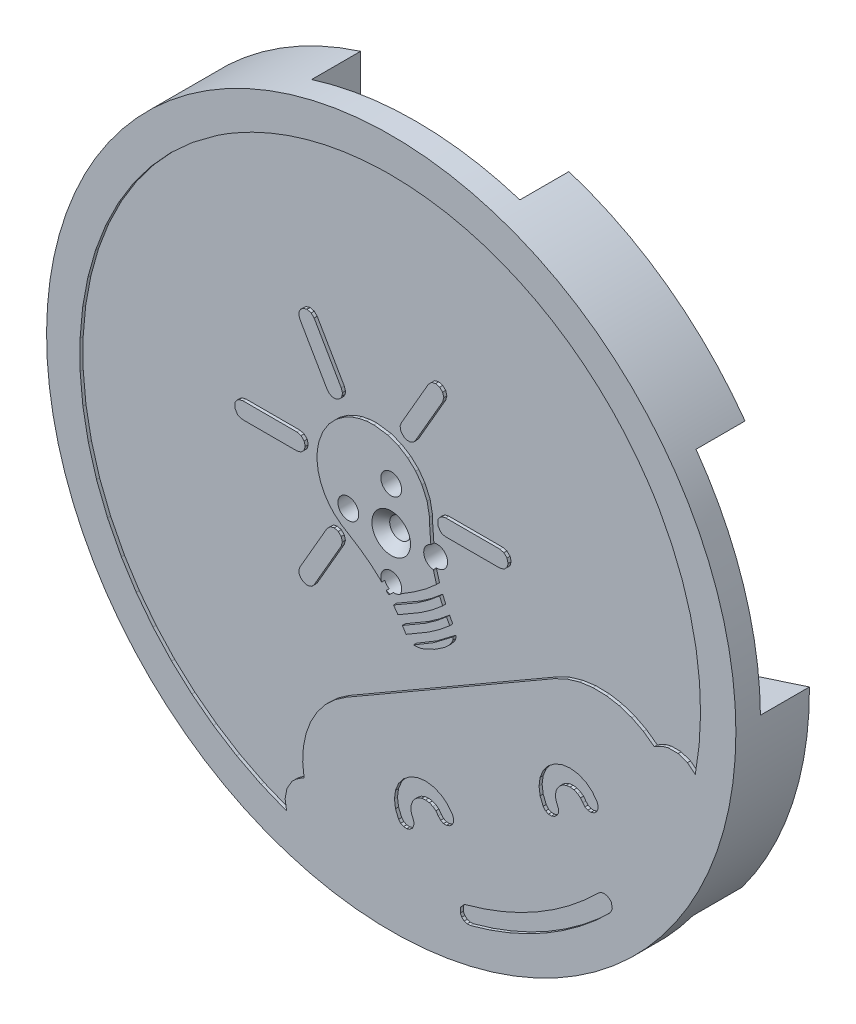
SolidWorks part; units mm, degrees
ref_plane "Front Plane" through (0, 0, 0) normal (0, 0, 1) x (1, 0, 0)
ref_plane "Top Plane" through (0, 0, 0) normal (0, 1, 0) x (1, 0, 0)
ref_plane "Right Plane" through (0, 0, 0) normal (1, 0, 0) x (0, 0, -1)
sketch "Sketch2" plane through (0, 0, 0) normal (0, 0, 1) x (1, 0, 0)
  line L0 (0, 10) -> (0, 0) construction
  line L1 (0, 0) -> (0, -10) construction
  line L3 (0, -10) -> (0, -56.25) construction
  line L4 (-56.25, 0) -> (-10, 0) construction
  line L5 (-10, 0) -> (0, 0) construction
  line L6 (0, 0) -> (10, 0) construction
  line L7 (10, 0) -> (56.25, 0) construction
  line L8 (0, 56.25) -> (0, 34.65) construction
  line L9 (0, 34.65) -> (0, 10) construction
  circle A0 centre (0, 0) radius 56.25
  point P6 (0, -33.125)
  point P8 (0, 34.65)
  point P13 (-33.125, 0)
  point P14 (33.125, 0)
  dimension "D1" = 112.5
  dimension "D2" = 20
  dimension "D3" = 21.6
extrude "Boss-Extrude1" add sketch "Sketch2" along normal blind 12
sketch "Sketch3" plane through (0, 0, 0) normal (0, 0, -1) x (-1, 0, 0)
  line L1 (-17, 34.65) -> (-17, 53.6196)
  line L2 (17, 34.65) -> (17, 53.6196)
  arc A0 (-17, 34.65) -> (17, 34.65) centre (0, 34.65) ccw
  circle A2 centre (0, 0) radius 56.25 construction
  arc A10 (17, 53.6196) -> (-17, 53.6196) centre (0, 0) ccw
  dimension "D1" = 34
sketch "Sketch4" plane through (0, 0, 0) normal (0, 0, -1) x (-1, 0, 0)
  line L0 (-10, 0) -> (-7, 0) construction
  line L1 (-7, 0) -> (0, 0) construction
  line L2 (0, 0) -> (7, 0) construction
  line L3 (7, 0) -> (10, 0) construction
  line L4 (0, -10) -> (0, -7) construction
  line L5 (0, -7) -> (0, 0) construction
  line L6 (0, 0) -> (0, 7) construction
  line L7 (0, 7) -> (0, 10) construction
  circle A0 centre (0, 0) radius 10
  dimension "D1" = 20
  dimension "D2" = 14
extrude "Cut-Extrude2" cut sketch "Sketch4" against normal blind 2
hole_wizard "M3 Clearance Hole1" positions "Sketch5" profile "Sketch6" hole size "M3" standard "ANSI Metric"
sketch "Sketch5" plane through (0, 0, 2) normal (0, 0, -1) x (-1, 0, 0)
  point P0 (7, 0)
  point P3 (0, 7)
  point P6 (-7, 0)
  point P9 (0, -7)
sketch "Sketch6" plane through (-7, 0, 2) normal (1, 0, 0) x (0, 1, 0)
  line L0 (0, 0) -> (0, 11.0215)
  line L1 (0, 11.0215) -> (1.7, 10)
  line L2 (1.7, 10) -> (1.7, 0)
  line L5 (1.7, 0) -> (0, 0)
  line L10 (0, 11.0215) -> (-1.7, 10) construction
  line L11 (0, -6.35) -> (0, 107.95) construction
  dimension "Hole Dia." = 3.4
  dimension "Hole Depth" = 10
  dimension "Drill Angle" = 118
hole_wizard "CSK for M3 Flat Head Machine Screw2" positions "Sketch9" profile "Sketch10" countersink size "M3" standard "ANSI Metric"
sketch "Sketch9" plane through (0, 0, 12) normal (0, 0, 1) x (1, 0, 0)
  point P0 (0, 0)
sketch "Sketch10" plane through (0, 0, 12) normal (1, 0, 0) x (0, -1, 0)
  line L0 (0, 0) -> (0, 11.0215)
  line L1 (0, 11.0215) -> (1.7, 10)
  line L2 (1.7, 10) -> (1.7, 1.45)
  line L3 (1.7, 1.45) -> (3.15, 0)
  line L5 (3.15, 0) -> (0, 0)
  line L6 (-1.7, 1.45) -> (-3.15, 0) construction
  line L10 (0, 11.0215) -> (-1.7, 10) construction
  line L11 (0, -6.35) -> (0, 107.95) construction
  dimension "Hole Dia." = 3.4
  dimension "Hole Depth" = 10
  dimension "Near C'Sink Dia." = 6.3
  dimension "Near C'Sink Angle" = 90
  dimension "Drill Angle" = 118
extrude "Cut-Extrude3" cut sketch "Sketch3" against normal blind 8
pattern_circular "CirPattern1" count 5 over 360 about axis through (0, 0, 0) along (0, 0, 1) of "Cut-Extrude3"
sketch "Sketch11" plane through (0, 0, 8) normal (0, 0, -1) x (-1, 0, 0)
  circle A0 centre (0, 34.65) radius 5.25
  dimension "D1" = 10.5
extrude "Cut-Extrude4" cut sketch "Sketch11" against normal blind 2.5
sketch "Sketch12" plane through (0, 0, 12) normal (0, 0, 1) x (1, 0, 0)
  line L0 (43.7235, 25.2994) -> (42.8623, 26.7358)
  line L1 (42.8623, 26.7358) -> (41.9454, 28.1541)
  line L2 (41.9454, 28.1541) -> (40.1116, 30.7156)
  line L3 (40.1116, 30.7156) -> (38.1348, 33.1435)
  line L4 (38.1348, 33.1435) -> (36.0227, 35.4332)
  line L5 (36.0227, 35.4332) -> (33.7829, 37.5804)
  line L6 (33.7829, 37.5804) -> (31.4231, 39.5807)
  line L7 (31.4231, 39.5807) -> (28.9511, 41.4296)
  line L8 (28.9511, 41.4296) -> (26.3743, 43.1228)
  line L9 (26.3743, 43.1228) -> (23.7005, 44.6558)
  line L10 (23.7005, 44.6558) -> (20.9373, 46.0242)
  line L11 (20.9373, 46.0242) -> (18.0925, 47.2236)
  line L12 (18.0925, 47.2236) -> (15.1736, 48.2497)
  line L13 (15.1736, 48.2497) -> (12.1883, 49.0979)
  line L14 (12.1883, 49.0979) -> (9.1442, 49.7639)
  line L15 (9.1442, 49.7639) -> (6.0491, 50.2433)
  line L16 (6.0491, 50.2433) -> (2.9106, 50.5316)
  line L17 (2.9106, 50.5316) -> (-0.2637, 50.6245)
  line L18 (-0.2637, 50.6245) -> (-1.3593, 50.6106)
  line L19 (-1.3593, 50.6106) -> (-4.53, 50.4362)
  line L20 (-4.53, 50.4362) -> (-7.6743, 50.0649)
  line L21 (-7.6743, 50.0649) -> (-10.7834, 49.4994)
  line L22 (-10.7834, 49.4994) -> (-13.8483, 48.742)
  line L23 (-13.8483, 48.742) -> (-16.86, 47.7953)
  line L24 (-16.86, 47.7953) -> (-19.8098, 46.6618)
  line L25 (-19.8098, 46.6618) -> (-22.6886, 45.344)
  line L26 (-22.6886, 45.344) -> (-25.4876, 43.8444)
  line L27 (-25.4876, 43.8444) -> (-25.5072, 43.8331)
  line L28 (-25.5072, 43.8331) -> (-25.5139, 43.8293)
  line L29 (-25.5139, 43.8293) -> (-26.569, 43.2016)
  line L30 (-26.569, 43.2016) -> (-26.7302, 43.1028)
  line L31 (-26.7302, 43.1028) -> (-27.5612, 42.5798)
  line L32 (-27.5612, 42.5798) -> (-27.5669, 42.5765)
  line L33 (-27.5669, 42.5765) -> (-28.0151, 42.2833)
  line L34 (-28.0151, 42.2833) -> (-28.4549, 41.9912)
  line L35 (-28.4549, 41.9912) -> (-32.4156, 39.0373)
  line L36 (-32.4156, 39.0373) -> (-36.011, 35.7728)
  line L37 (-36.011, 35.7728) -> (-39.2342, 32.2285)
  line L38 (-39.2342, 32.2285) -> (-42.0781, 28.435)
  line L39 (-42.0781, 28.435) -> (-44.5355, 24.4229)
  line L40 (-44.5355, 24.4229) -> (-46.5993, 20.2229)
  line L41 (-46.5993, 20.2229) -> (-48.2626, 15.8657)
  line L42 (-48.2626, 15.8657) -> (-49.5181, 11.3819)
  line L43 (-49.5181, 11.3819) -> (-50.3588, 6.8022)
  line L44 (-50.3588, 6.8022) -> (-50.7776, 2.1572)
  line L45 (-50.7776, 2.1572) -> (-50.7675, -2.5225)
  line L46 (-50.7675, -2.5225) -> (-50.3212, -7.2061)
  line L47 (-50.3212, -7.2061) -> (-49.4318, -11.863)
  line L48 (-49.4318, -11.863) -> (-48.0921, -16.4626)
  line L49 (-48.0921, -16.4626) -> (-46.2951, -20.9742)
  line L50 (-46.2951, -20.9742) -> (-44.0336, -25.3672)
  line L51 (-44.0336, -25.3672) -> (-41.6099, -29.1646)
  line L52 (-41.6099, -29.1646) -> (-38.8754, -32.7114)
  line L53 (-38.8754, -32.7114) -> (-35.8505, -35.9908)
  line L54 (-35.8505, -35.9908) -> (-32.5551, -38.9862)
  line L55 (-32.5551, -38.9862) -> (-29.0095, -41.6806)
  line L56 (-29.0095, -41.6806) -> (-25.2338, -44.0575)
  line L57 (-25.2338, -44.0575) -> (-21.2482, -46.1)
  line L58 (-21.2482, -46.1) -> (-17.0728, -47.7914)
  line L59 (-17.0728, -47.7914) -> (-17.32, -46.1638)
  line L60 (-17.32, -46.1638) -> (-17.0163, -44.577)
  line L61 (-17.0163, -44.577) -> (-16.1985, -43.1708)
  line L62 (-16.1985, -43.1708) -> (-15.6084, -42.5793)
  line L63 (-15.6084, -42.5793) -> (-14.9035, -42.0854)
  line L64 (-14.9035, -42.0854) -> (-14.2254, -41.6946)
  line L65 (-14.2254, -41.6946) -> (-14.4481, -39.532)
  line L66 (-14.4481, -39.532) -> (-14.3405, -37.3819)
  line L67 (-14.3405, -37.3819) -> (-13.9125, -35.2814)
  line L68 (-13.9125, -35.2814) -> (-13.1741, -33.2679)
  line L69 (-13.1741, -33.2679) -> (-12.1352, -31.3787)
  line L70 (-12.1352, -31.3787) -> (-10.8059, -29.6512)
  line L71 (-10.8059, -29.6512) -> (-9.1961, -28.1226)
  line L72 (-9.1961, -28.1226) -> (-7.3158, -26.8303)
  line L73 (-7.3158, -26.8303) -> (26.5969, -7.2521)
  line L74 (26.5969, -7.2521) -> (28.6562, -6.2697)
  line L75 (28.6562, -6.2697) -> (30.7847, -5.6397)
  line L76 (30.7847, -5.6397) -> (32.9452, -5.352)
  line L77 (32.9452, -5.352) -> (35.1004, -5.3966)
  line L78 (35.1004, -5.3966) -> (37.2131, -5.7635)
  line L79 (37.2131, -5.7635) -> (39.2459, -6.4429)
  line L80 (39.2459, -6.4429) -> (41.1616, -7.4246)
  line L81 (41.1616, -7.4246) -> (42.923, -8.6987)
  line L82 (42.923, -8.6987) -> (43.6019, -8.308)
  line L83 (43.6019, -8.308) -> (44.3813, -7.9447)
  line L84 (44.3813, -7.9447) -> (45.1879, -7.7291)
  line L85 (45.1879, -7.7291) -> (46.813, -7.7223)
  line L86 (46.813, -7.7223) -> (48.338, -8.2503)
  line L87 (48.338, -8.2503) -> (49.6234, -9.2755)
  line L88 (49.6234, -9.2755) -> (50.251, -4.8179)
  line L89 (50.251, -4.8179) -> (50.4804, -0.3486)
  line L90 (50.4804, -0.3486) -> (50.316, 4.1065)
  line L91 (50.316, 4.1065) -> (49.7622, 8.5218)
  line L92 (49.7622, 8.5218) -> (48.8234, 12.8715)
  line L93 (48.8234, 12.8715) -> (47.5039, 17.1299)
  line L94 (47.5039, 17.1299) -> (45.8082, 21.2713)
  line L95 (45.8082, 21.2713) -> (43.7406, 25.2698)
  line L96 (43.7406, 25.2698) -> (43.7235, 25.2994)
  line L97 (18.8919, 5.9467) -> (19.0715, 5.2506)
  line L98 (19.0715, 5.2506) -> (18.8841, 4.5994)
  line L99 (18.8841, 4.5994) -> (18.4047, 4.1205)
  line L100 (18.4047, 4.1205) -> (17.7085, 3.9415)
  line L101 (17.7085, 3.9415) -> (8.9061, 3.9412)
  line L102 (8.9061, 3.9412) -> (8.4238, 4.017)
  line L103 (8.4238, 4.017) -> (8.0375, 4.2346)
  line L104 (8.0375, 4.2346) -> (7.5907, 4.9484)
  line L105 (7.5907, 4.9484) -> (7.6407, 5.789)
  line L106 (7.6407, 5.789) -> (7.8754, 6.1652)
  line L107 (7.8754, 6.1652) -> (8.2623, 6.463)
  line L108 (8.2623, 6.463) -> (8.8865, 6.6177)
  line L109 (8.8865, 6.6177) -> (8.9065, 6.6172)
  line L110 (8.9065, 6.6172) -> (17.7069, 6.6177)
  line L111 (17.7069, 6.6177) -> (18.3911, 6.4443)
  line L112 (18.3911, 6.4443) -> (18.8918, 5.9468)
  line L113 (18.8918, 5.9468) -> (18.8919, 5.9467)
  line L114 (8.3841, 24.1347) -> (8.5767, 23.4467)
  line L115 (8.5767, 23.4467) -> (8.3879, 22.7576)
  line L116 (8.3879, 22.7576) -> (3.9874, 15.1352)
  line L117 (3.9874, 15.1352) -> (3.5976, 14.6654)
  line L118 (3.5976, 14.6654) -> (3.1217, 14.4439)
  line L119 (3.1217, 14.4439) -> (2.617, 14.4375)
  line L120 (2.617, 14.4375) -> (2.141, 14.6132)
  line L121 (2.141, 14.6132) -> (1.7509, 14.9378)
  line L122 (1.7509, 14.9378) -> (1.5042, 15.3782)
  line L123 (1.5042, 15.3782) -> (1.4583, 15.9011)
  line L124 (1.4583, 15.9011) -> (1.6706, 16.4735)
  line L125 (1.6706, 16.4735) -> (6.0707, 24.0956)
  line L126 (6.0707, 24.0956) -> (6.6071, 24.6229)
  line L127 (6.6071, 24.6229) -> (7.2307, 24.7818)
  line L128 (7.2307, 24.7818) -> (7.249, 24.781)
  line L129 (7.249, 24.781) -> (7.9008, 24.6058)
  line L130 (7.9008, 24.6058) -> (8.3841, 24.1347)
  line L131 (33.5794, -21.1232) -> (32.7665, -20.0667)
  line L132 (32.7665, -20.0667) -> (31.7242, -19.2693)
  line L133 (31.7242, -19.2693) -> (30.5123, -18.7655)
  line L134 (30.5123, -18.7655) -> (29.1908, -18.5899)
  line L135 (29.1908, -18.5899) -> (27.8691, -18.7655)
  line L136 (27.8691, -18.7655) -> (26.6569, -19.2694)
  line L137 (26.6569, -19.2694) -> (25.6142, -20.067)
  line L138 (25.6142, -20.067) -> (24.8011, -21.1236)
  line L139 (24.8011, -21.1236) -> (24.2926, -22.356)
  line L140 (24.2926, -22.356) -> (24.1233, -23.6576)
  line L141 (24.1233, -23.6576) -> (24.293, -24.9592)
  line L142 (24.293, -24.9592) -> (24.8017, -26.1916)
  line L143 (24.8017, -26.1916) -> (25.1928, -26.6515)
  line L144 (25.1928, -26.6515) -> (25.6667, -26.8677)
  line L145 (25.6667, -26.8677) -> (26.1675, -26.8724)
  line L146 (26.1675, -26.8724) -> (26.6394, -26.6979)
  line L147 (26.6394, -26.6979) -> (27.0265, -26.3765)
  line L148 (27.0265, -26.3765) -> (27.2728, -25.9404)
  line L149 (27.2728, -25.9404) -> (27.3226, -25.4219)
  line L150 (27.3226, -25.4219) -> (27.1198, -24.8532)
  line L151 (27.1198, -24.8532) -> (26.8788, -24.271)
  line L152 (26.8788, -24.271) -> (26.7984, -23.6577)
  line L153 (26.7984, -23.6577) -> (26.8785, -23.0444)
  line L154 (26.8785, -23.0444) -> (27.1192, -22.4622)
  line L155 (27.1192, -22.4622) -> (27.5031, -21.9625)
  line L156 (27.5031, -21.9625) -> (27.9943, -21.5862)
  line L157 (27.9943, -21.5862) -> (28.5658, -21.3489)
  line L158 (28.5658, -21.3489) -> (29.1905, -21.2664)
  line L159 (29.1905, -21.2664) -> (29.8152, -21.3489)
  line L160 (29.8152, -21.3489) -> (30.3865, -21.5861)
  line L161 (30.3865, -21.5861) -> (30.8776, -21.9623)
  line L162 (30.8776, -21.9623) -> (31.2614, -22.4621)
  line L163 (31.2614, -22.4621) -> (31.6154, -22.872)
  line L164 (31.6154, -22.872) -> (32.084, -23.1026)
  line L165 (32.084, -23.1026) -> (32.6051, -23.137)
  line L166 (32.6051, -23.137) -> (33.1164, -22.9587)
  line L167 (33.1164, -22.9587) -> (33.5098, -22.6012)
  line L168 (33.5098, -22.6012) -> (33.728, -22.1368)
  line L169 (33.728, -22.1368) -> (33.7561, -21.6244)
  line L170 (33.7561, -21.6244) -> (33.5792, -21.1232)
  line L171 (33.5792, -21.1232) -> (33.5794, -21.1232)
  line L172 (35.9136, -34.2086) -> (35.7019, -33.9343)
  line L173 (35.7019, -33.9343) -> (35.2582, -33.6402)
  line L174 (35.2582, -33.6402) -> (34.7536, -33.5425)
  line L175 (34.7536, -33.5425) -> (34.2493, -33.6411)
  line L176 (34.2493, -33.6411) -> (33.8061, -33.936)
  line L177 (33.8061, -33.936) -> (31.499, -36.0991)
  line L178 (31.499, -36.0991) -> (29.0626, -38.0994)
  line L179 (29.0626, -38.0994) -> (26.5058, -39.9318)
  line L180 (26.5058, -39.9318) -> (23.8373, -41.5911)
  line L181 (23.8373, -41.5911) -> (21.066, -43.0723)
  line L182 (21.066, -43.0723) -> (18.2006, -44.3703)
  line L183 (18.2006, -44.3703) -> (15.2501, -45.48)
  line L184 (15.2501, -45.48) -> (12.2231, -46.3963)
  line L185 (12.2231, -46.3963) -> (11.8899, -46.5358)
  line L186 (11.8899, -46.5358) -> (11.3288, -47.1827)
  line L187 (11.3288, -47.1827) -> (11.2738, -48.0372)
  line L188 (11.2738, -48.0372) -> (11.5102, -48.5142)
  line L189 (11.5102, -48.5142) -> (11.8976, -48.8517)
  line L190 (11.8976, -48.8517) -> (12.3834, -49.0194)
  line L191 (12.3834, -49.0194) -> (12.9147, -48.9866)
  line L192 (12.9147, -48.9866) -> (16.1107, -48.0191)
  line L193 (16.1107, -48.0191) -> (19.226, -46.8474)
  line L194 (19.226, -46.8474) -> (22.2515, -45.4768)
  line L195 (22.2515, -45.4768) -> (25.1777, -43.9128)
  line L196 (25.1777, -43.9128) -> (27.9953, -42.1608)
  line L197 (27.9953, -42.1608) -> (30.6951, -40.2261)
  line L198 (30.6951, -40.2261) -> (33.2676, -38.114)
  line L199 (33.2676, -38.114) -> (35.7035, -35.8301)
  line L200 (35.7035, -35.8301) -> (36.0844, -35.0551)
  line L201 (36.0844, -35.0551) -> (35.9136, -34.2086)
  line L202 (5.0001, 9.3752) -> (5.8508, 7.4638)
  line L203 (5.8508, 7.4638) -> (6.2496, 5.3897)
  line L204 (6.2496, 5.3897) -> (6.2659, 4.2834)
  line L205 (6.2659, 4.2834) -> (6.5775, -0.0444)
  line L206 (6.5775, -0.0444) -> (6.9114, -1.8586)
  line L207 (6.9114, -1.8586) -> (7.3817, -3.5473)
  line L208 (7.3817, -3.5473) -> (5.6898, -5.0138)
  line L209 (5.6898, -5.0138) -> (3.6505, -6.4723)
  line L210 (3.6505, -6.4723) -> (1.5139, -7.7977)
  line L211 (1.5139, -7.7977) -> (-0.4701, -8.8653)
  line L212 (-0.4701, -8.8653) -> (-1.7709, -7.4519)
  line L213 (-1.7709, -7.4519) -> (-3.2631, -6.1237)
  line L214 (-3.2631, -6.1237) -> (-5.0314, -4.8121)
  line L215 (-5.0314, -4.8121) -> (-7.1608, -3.4481)
  line L216 (-7.1608, -3.4481) -> (-8.109, -2.8817)
  line L217 (-8.109, -2.8817) -> (-9.2084, -1.9979)
  line L218 (-9.2084, -1.9979) -> (-10.1514, -0.9657)
  line L219 (-10.1514, -0.9657) -> (-10.9252, 0.1926)
  line L220 (-10.9252, 0.1926) -> (-11.5166, 1.4545)
  line L221 (-11.5166, 1.4545) -> (-11.9128, 2.7976)
  line L222 (-11.9128, 2.7976) -> (-12.1007, 4.1994)
  line L223 (-12.1007, 4.1994) -> (-12.0674, 5.6375)
  line L224 (-12.0674, 5.6375) -> (-11.7999, 7.0895)
  line L225 (-11.7999, 7.0895) -> (-11.1395, 8.8296)
  line L226 (-11.1395, 8.8296) -> (-10.174, 10.358)
  line L227 (-10.174, 10.358) -> (-8.9501, 11.6473)
  line L228 (-8.9501, 11.6473) -> (-7.5146, 12.6703)
  line L229 (-7.5146, 12.6703) -> (-6.4277, 13.206)
  line L230 (-6.4277, 13.206) -> (-5.275, 13.596)
  line L231 (-5.275, 13.596) -> (-4.0716, 13.8317)
  line L232 (-4.0716, 13.8317) -> (-2.8328, 13.9043)
  line L233 (-2.8328, 13.9043) -> (-0.5397, 13.5906)
  line L234 (-0.5397, 13.5906) -> (1.182, 12.9399)
  line L235 (1.182, 12.9399) -> (2.6961, 11.9911)
  line L236 (2.6961, 11.9911) -> (3.9773, 10.7881)
  line L237 (3.9773, 10.7881) -> (5.0001, 9.3752)
  line L238 (7.8894, -4.9172) -> (8.395, -6.0631)
  line L239 (8.395, -6.0631) -> (6.7815, -7.4143)
  line L240 (6.7815, -7.4143) -> (4.8994, -8.7462)
  line L241 (4.8994, -8.7462) -> (1.0949, -10.9729)
  line L242 (1.0949, -10.9729) -> (0.3738, -9.9489)
  line L243 (0.3738, -9.9489) -> (4.2522, -7.7051)
  line L244 (4.2522, -7.7051) -> (6.1793, -6.3429)
  line L245 (6.1793, -6.3429) -> (7.8894, -4.9172)
  line L246 (9.0128, -7.3161) -> (9.5437, -8.2953)
  line L247 (9.5437, -8.2953) -> (7.9562, -9.6109)
  line L248 (7.9562, -9.6109) -> (6.1212, -10.9052)
  line L249 (6.1212, -10.9052) -> (2.4134, -13.0803)
  line L250 (2.4134, -13.0803) -> (1.8236, -12.116)
  line L251 (1.8236, -12.116) -> (5.5241, -9.9638)
  line L252 (5.5241, -9.9638) -> (7.3622, -8.6707)
  line L253 (7.3622, -8.6707) -> (9.0128, -7.3161)
  line L254 (10.0917, -9.6039) -> (10.0514, -10.0863)
  line L255 (10.0514, -10.0863) -> (9.8604, -10.5394)
  line L256 (9.8604, -10.5394) -> (9.3329, -11.2211)
  line L257 (9.3329, -11.2211) -> (8.7178, -11.7755)
  line L258 (8.7178, -11.7755) -> (7.2524, -12.7612)
  line L259 (7.2524, -12.7612) -> (7.1244, -12.8351)
  line L260 (7.1244, -12.8351) -> (5.538, -13.6113)
  line L261 (5.538, -13.6113) -> (4.7504, -13.8668)
  line L262 (4.7504, -13.8668) -> (3.8962, -13.9828)
  line L263 (3.8962, -13.9828) -> (3.6375, -13.968)
  line L264 (3.6375, -13.968) -> (6.9737, -11.9709)
  line L265 (6.9737, -11.9709) -> (10.0917, -9.6039)
  line L266 (-12.5879, 24.1326) -> (-12.5667, 24.0958)
  line L267 (-12.5667, 24.0958) -> (-8.1661, 16.4737)
  line L268 (-8.1661, 16.4737) -> (-7.9633, 15.905)
  line L269 (-7.9633, 15.905) -> (-8.013, 15.3865)
  line L270 (-8.013, 15.3865) -> (-8.2594, 14.9504)
  line L271 (-8.2594, 14.9504) -> (-8.6464, 14.629)
  line L272 (-8.6464, 14.629) -> (-9.1183, 14.4545)
  line L273 (-9.1183, 14.4545) -> (-9.6192, 14.4592)
  line L274 (-9.6192, 14.4592) -> (-10.0931, 14.6754)
  line L275 (-10.0931, 14.6754) -> (-10.4842, 15.1353)
  line L276 (-10.4842, 15.1353) -> (-14.8848, 22.7575)
  line L277 (-14.8848, 22.7575) -> (-15.0614, 23.2586)
  line L278 (-15.0614, 23.2586) -> (-15.0331, 23.7708)
  line L279 (-15.0331, 23.7708) -> (-14.8149, 24.2351)
  line L280 (-14.8149, 24.2351) -> (-14.4218, 24.5925)
  line L281 (-14.4218, 24.5925) -> (-13.787, 24.7807)
  line L282 (-13.787, 24.7807) -> (-13.7211, 24.7813)
  line L283 (-13.7211, 24.7813) -> (-13.0701, 24.6045)
  line L284 (-13.0701, 24.6045) -> (-12.5879, 24.1326)
  line L285 (9.9823, -34.7477) -> (9.1692, -33.691)
  line L286 (9.1692, -33.691) -> (8.1265, -32.8933)
  line L287 (8.1265, -32.8933) -> (6.9143, -32.3893)
  line L288 (6.9143, -32.3893) -> (5.5927, -32.2136)
  line L289 (5.5927, -32.2136) -> (4.2712, -32.3893)
  line L290 (4.2712, -32.3893) -> (3.0594, -32.8931)
  line L291 (3.0594, -32.8931) -> (2.0171, -33.6907)
  line L292 (2.0171, -33.6907) -> (1.2042, -34.7473)
  line L293 (1.2042, -34.7473) -> (0.6956, -35.9797)
  line L294 (0.6956, -35.9797) -> (0.5259, -37.2815)
  line L295 (0.5259, -37.2815) -> (0.6954, -38.5834)
  line L296 (0.6954, -38.5834) -> (1.204, -39.8158)
  line L297 (1.204, -39.8158) -> (1.5497, -40.2189)
  line L298 (1.5497, -40.2189) -> (2.0071, -40.4503)
  line L299 (2.0071, -40.4503) -> (2.5179, -40.4934)
  line L300 (2.5179, -40.4934) -> (3.0236, -40.3316)
  line L301 (3.0236, -40.3316) -> (3.434, -39.9782)
  line L302 (3.434, -39.9782) -> (3.6651, -39.5098)
  line L303 (3.6651, -39.5098) -> (3.7002, -38.9888)
  line L304 (3.7002, -38.9888) -> (3.5225, -38.4772)
  line L305 (3.5225, -38.4772) -> (3.2817, -37.8949)
  line L306 (3.2817, -37.8949) -> (3.2013, -37.2815)
  line L307 (3.2013, -37.2815) -> (3.2816, -36.6682)
  line L308 (3.2816, -36.6682) -> (3.5225, -36.0859)
  line L309 (3.5225, -36.0859) -> (3.9062, -35.5862)
  line L310 (3.9062, -35.5862) -> (4.3971, -35.2101)
  line L311 (4.3971, -35.2101) -> (4.9682, -34.9731)
  line L312 (4.9682, -34.9731) -> (5.5928, -34.8906)
  line L313 (5.5928, -34.8906) -> (6.2175, -34.973)
  line L314 (6.2175, -34.973) -> (6.789, -35.2099)
  line L315 (6.789, -35.2099) -> (7.2801, -35.5859)
  line L316 (7.2801, -35.5859) -> (7.6639, -36.0855)
  line L317 (7.6639, -36.0855) -> (8.0545, -36.5484)
  line L318 (8.0545, -36.5484) -> (8.5289, -36.7663)
  line L319 (8.5289, -36.7663) -> (9.0308, -36.7716)
  line L320 (9.0308, -36.7716) -> (9.504, -36.5968)
  line L321 (9.504, -36.5968) -> (9.8921, -36.2746)
  line L322 (9.8921, -36.2746) -> (10.1387, -35.8373)
  line L323 (10.1387, -35.8373) -> (10.1875, -35.3175)
  line L324 (10.1875, -35.3175) -> (9.9823, -34.7477)
  line L325 (-14.2195, 5.9401) -> (-14.043, 5.2461)
  line L326 (-14.043, 5.2461) -> (-14.231, 4.5974)
  line L327 (-14.231, 4.5974) -> (-14.7089, 4.1202)
  line L328 (-14.7089, 4.1202) -> (-15.4021, 3.9405)
  line L329 (-15.4021, 3.9405) -> (-24.2036, 3.9406)
  line L330 (-24.2036, 3.9406) -> (-24.6867, 4.0159)
  line L331 (-24.6867, 4.0159) -> (-25.0736, 4.2335)
  line L332 (-25.0736, 4.2335) -> (-25.5208, 4.948)
  line L333 (-25.5208, 4.948) -> (-25.4702, 5.7896)
  line L334 (-25.4702, 5.7896) -> (-25.2348, 6.1659)
  line L335 (-25.2348, 6.1659) -> (-24.8467, 6.4635)
  line L336 (-24.8467, 6.4635) -> (-24.2225, 6.617)
  line L337 (-24.2225, 6.617) -> (-24.2032, 6.6167)
  line L338 (-24.2032, 6.6167) -> (-15.4008, 6.617)
  line L339 (-15.4008, 6.617) -> (-14.7176, 6.4401)
  line L340 (-14.7176, 6.4401) -> (-14.2195, 5.9401)
  line L341 (-8.1701, -4.5387) -> (-7.9778, -5.2265)
  line L342 (-7.9778, -5.2265) -> (-8.1665, -5.9153)
  line L343 (-8.1665, -5.9153) -> (-12.5661, -13.5371)
  line L344 (-12.5661, -13.5371) -> (-12.9596, -13.9757)
  line L345 (-12.9596, -13.9757) -> (-13.4289, -14.1804)
  line L346 (-13.4289, -14.1804) -> (-13.9213, -14.1816)
  line L347 (-13.9213, -14.1816) -> (-14.384, -14.0098)
  line L348 (-14.384, -14.0098) -> (-14.7645, -13.6953)
  line L349 (-14.7645, -13.6953) -> (-15.0099, -13.2685)
  line L350 (-15.0099, -13.2685) -> (-15.0677, -12.7598)
  line L351 (-15.0677, -12.7598) -> (-14.885, -12.1995)
  line L352 (-14.885, -12.1995) -> (-10.4844, -4.5771)
  line L353 (-10.4844, -4.5771) -> (-9.9476, -4.0495)
  line L354 (-9.9476, -4.0495) -> (-9.3233, -3.8928)
  line L355 (-9.3233, -3.8928) -> (-9.3054, -3.8919)
  line L356 (-9.3054, -3.8919) -> (-8.6537, -4.0675)
  line L357 (-8.6537, -4.0675) -> (-8.1705, -4.539)
  line L358 (-8.1705, -4.539) -> (-8.1701, -4.5387)
extrude "Cut-Extrude6" cut sketch "Sketch12" against normal blind 0.5
equation "\"board_length\"= 260mm"
equation "\"board_height\"= 200mm"
equation "\"board_width\"= 16.5mm"
equation "\"token_thickness\"= 7mm"
equation "\"token_diameter\"= 32mm"
equation "\"board_side_lower_height\"= 55mm"
equation "\"board_side_height\"= 156.5mm"
equation "\"board_side_length\"= 100mm"
equation "\"board_slot_width\"= \"board_length\" / 7"
equation "\"token_ridge\"= ( \"token_thickness\" - 4mm ) / 2"
equation "\"token_ridge_width\"= 1.5mm"
equation "\"25T_outer_diameter\"= 20mm"
equation "\"25T_inner_diameter\"= 9mm"
equation "\"2T_screw_distance\"= 14mm"
equation "\"2T_outer_thickness\"= 2mm"
equation "\"2T_inner_thickness\"= 4.5mm"
equation "\"D1@Sketch2\"=\"MG996R_outer_length\"*2+4.5mm"
equation "\"D2@Sketch2\"=\"25T_outer_diameter\""
equation "\"D1@Boss-Extrude1\"=\"dispenser_wheel_width\""
equation "\"D1@Sketch3\"=\"token_diameter\"+2.0mm"
equation "\"D1@Sketch4\"=\"25T_outer_diameter\""
equation "\"D1@Cut-Extrude2\"=\"2T_outer_thickness\""
equation "\"D2@Sketch4\"=\"2T_screw_distance\""
equation "\"MG996R_outer_length\"= 54mm"
equation "\"MG996R_inner_length\"= 40mm"
equation "\"MG996R_width\"= 20mm"
equation "\"MG996R_height\"= 26.6mm"
equation "\"MG996R_full_height\"= 45.7mm"
equation "\"MG996R_full_width\"= 55.5mm"
equation "\"MG996R_screw_distance\"= 10mm"
equation "\"D1@Cut-Extrude3\"=\"token_thickness\"+1mm"
equation "\"magnet_diameter\"= 10mm"
equation "\"D1@Sketch11\"=\"magnet_diameter\"+0.5mm"
equation "\"magnet_thickness\"= 2mm"
equation "\"D1@Cut-Extrude4\"=\"magnet_thickness\"+0.5mm"
equation "\"dispenser_barrel_margin\"= 2.5mm"
equation "\"dispenser_wheel_width\"= \"token_thickness\" + 5mm"
equation "\"D3@Sketch2\"=\"token_diameter\"/2*1.35"
